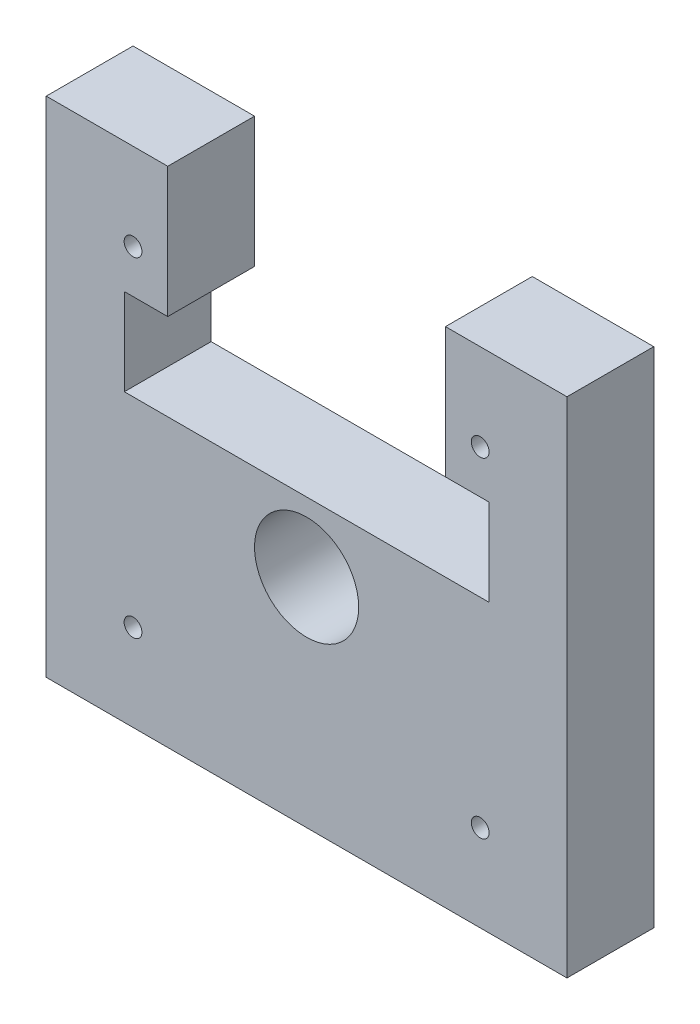
SolidWorks part; units mm, degrees
material "ABS"
ref_plane "Front Plane" through (0, 0, 0) normal (0, 0, 1) x (1, 0, 0)
ref_plane "Top Plane" through (0, 0, 0) normal (0, 1, 0) x (1, 0, 0)
ref_plane "Right Plane" through (0, 0, 0) normal (1, 0, 0) x (0, 0, -1)
sketch "Sketch1" plane through (0, 0, 0) normal (0, 0, 1) x (1, 0, 0)
  line L0 (-30, 33) -> (30, 33)
  line L1 (-20, 23) -> (20, 23) construction
  line L2 (-20, 23) -> (-20, -15) construction
  line L3 (-20, -15) -> (20, -15) construction
  line L4 (20, 23) -> (20, -15) construction
  line L5 (30, 33) -> (30, -25)
  line L6 (-30, -25) -> (30, -25)
  line L7 (-30, 33) -> (-30, -25)
  line L8 (-21, 18) -> (21, 18)
  line L9 (-19, 16) -> (19, 16) construction
  line L10 (-19, 16) -> (-19, 10) construction
  line L11 (-19, 10) -> (19, 10) construction
  line L12 (19, 16) -> (19, 10) construction
  line L13 (21, 18) -> (21, 8)
  line L14 (-21, 8) -> (21, 8)
  line L15 (-21, 18) -> (-21, 8)
  line L17 (-24, -24) -> (24, -24) construction
  line L18 (-24, -24) -> (-24, 24) construction
  line L19 (-24, 24) -> (24, 24) construction
  line L20 (24, -24) -> (24, 24) construction
  line L21 (-24, -24) -> (24, 24) construction
  line L22 (-24, 24) -> (24, -24) construction
  circle A0 centre (0, 0) radius 6
  point P15 (0, 10)
  point P20 (27.1193, -21.8297)
  point P25 (-24.7677, -25.6226)
  point P26 (-23.9175, 23.9175)
  dimension "D4" = 20
  dimension "D5" = 12
  dimension "D11" = 6
  dimension "D1" = 23
  dimension "D2" = 15
  dimension "D3" = 20
  dimension "D7" = 7
  dimension "D8" = 6
  dimension "D9" = 38
  dimension "D6" = 10
  dimension "D10" = 2
extrude "Boss-Extrude1" add sketch "Sketch1" along normal blind 10 contours L0 L7 L6 L5 A0 L15 L8 L13 L14 | L8 L15 L14 L13
sketch "Sketch2" plane through (0, 0, 10) normal (0, 0, 1) x (1, 0, 0)
  point P0 (20, 23)
  point P3 (-20, 23)
  point P6 (-20, -15)
  point P9 (20, -15)
hole_wizard "M2.5x0.45 Tapped Hole1" positions "Sketch2" profile "Sketch3" tap size "M2.5x0.45" standard "ANSI Metric" end condition through all
sketch "Sketch3" plane through (20, 23, 10) normal (1, 0, 0) x (0, -1, 0)
  line L0 (0, 0) -> (0, 10)
  line L1 (0, 10) -> (1.025, 10)
  line L2 (1.025, 10) -> (1.025, 0)
  line L5 (1.025, 0) -> (0, 0)
  line L11 (0, -6.35) -> (0, 107.95) construction
  dimension "Thru Tap Drill Dia." = 2.05
  dimension "Thru Tap Drill Depth" = 10
cosmetic thread "Hole Thread1" parameters "D2"=2.5
cosmetic thread "Hole Thread2" parameters "D2"=2.5
cosmetic thread "Hole Thread3" parameters "D2"=2.5
cosmetic thread "Hole Thread4" parameters "D2"=2.5
sketch "Sketch4" plane through (0, 0, 0) normal (0, 0, 1) x (1, 0, 0)
  line L0 (-30, 33) -> (30, 33) construction
  line L1 (-16, 33) -> (16, 33)
  line L2 (-16, 33) -> (-16, 18)
  line L3 (-16, 18) -> (16, 18)
  line L4 (16, 33) -> (16, 18)
  line L5 (-21, 18) -> (21, 18) construction
  line L6 (21, 18) -> (21, 8) construction
  line L7 (-21, 8) -> (21, 8) construction
  line L8 (-21, 18) -> (-21, 8) construction
  line L9 (21, 18) -> (21, 8)
  line L10 (-21, 8) -> (21, 8)
  line L11 (-21, 18) -> (-21, 8)
  line L12 (-21, 18) -> (21, 18)
  point P8 (0, 33)
  dimension "D1" = 32
extrude "Cut-Extrude1" cut sketch "Sketch4" against normal through all both and the other way through all contours L4 L1 L2 L3 | L12 L11 L10 L9 L3
